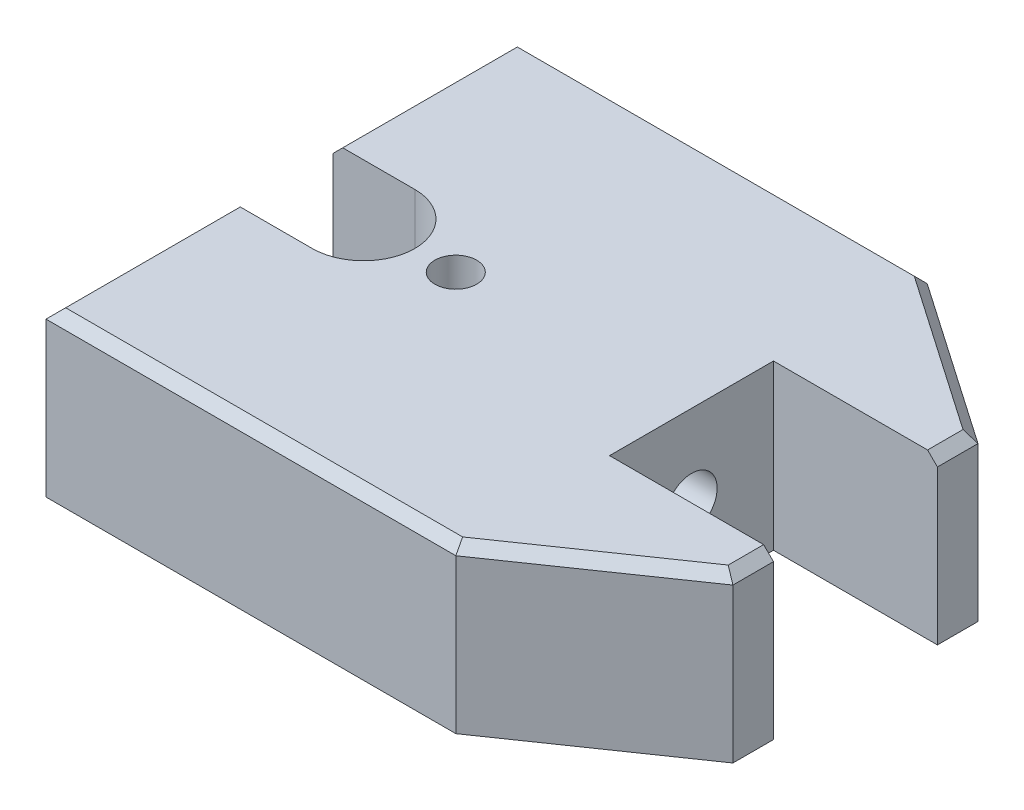
SolidWorks part; units mm, degrees
ref_plane "Front Plane" through (0, 0, 0) normal (0, 0, 1) x (1, 0, 0)
ref_plane "Top Plane" through (0, 0, 0) normal (0, 1, 0) x (1, 0, 0)
ref_plane "Right Plane" through (0, 0, 0) normal (1, 0, 0) x (0, 0, -1)
sketch "Sketch2" plane through (0, 0, 0) normal (0, 1, 0) x (1, 0, 0)
  line L0 (0, 0) -> (-73.0604, 0) construction
  line L1 (0, 36.5125) -> (0, -36.5125)
  line L2 (0, -36.5125) -> (63.5, -36.5125)
  line L3 (0, 36.5125) -> (63.5, 36.5125)
  line L4 (63.5, -36.5125) -> (88.9, -18.9865)
  line L5 (63.5, 36.5125) -> (88.9, 18.9865)
  line L6 (88.9, -18.9865) -> (88.9, 18.9865)
  point P9 (88.9, 0)
  dimension "D1" = 63.5
  dimension "D2" = 73.025
  dimension "D3" = 88.9
  dimension "D4" = 17.526
extrude "Boss-Extrude2" add sketch "Sketch2" along normal mid plane 25.4
sketch "Sketch3" plane through (0, 12.7, 0) normal (0, 1, 0) x (1, 0, 0)
  line L0 (0, 0) -> (88.9, 0) construction
  line L1 (88.9, -18.9865) -> (88.9, 18.9865) construction
  line L3 (63.5, 12.7) -> (88.9, 12.7)
  line L4 (63.5, 12.7) -> (63.5, -12.7)
  line L5 (63.5, -12.7) -> (88.9, -12.7)
  line L6 (88.9, 12.7) -> (88.9, -12.7)
  line L7 (63.5, 12.7) -> (88.9, -12.7) construction
  line L8 (63.5, -12.7) -> (88.9, 12.7) construction
  point P5 (76.2, 0)
  dimension "D1" = 25.4
  dimension "D2" = 25.4
extrude "Cut-Extrude1" cut sketch "Sketch3" against normal through all
sketch "Sketch4" plane through (0, 12.7, 0) normal (0, 1, 0) x (1, 0, 0)
  line L0 (0, 7.9375) -> (12.6873, 7.9375)
  line L1 (0, 36.5125) -> (0, -36.5125) construction
  line L2 (12.6873, -7.9375) -> (0, -7.9375)
  line L3 (0, -7.9375) -> (0, 7.9375)
  arc A0 (12.6873, 7.9375) -> (12.6873, -7.9375) centre (12.6873, 0) cw
  point P4 (20.6248, 0)
  dimension "D1" = 20.6248
  dimension "D2" = 15.875
extrude "Cut-Extrude3" cut sketch "Sketch4" against normal through all
hole_wizard "Hole1" positions "Sketch5" profile "Sketch6" legacy
sketch "Sketch5" plane through (0, 12.7, 0) normal (0, 1, 0) x (1, 0, 0)
  line L0 (0, -7.9375) -> (0, -36.5125) construction
  point P0 (26.9748, 0)
  dimension "D1" = 26.9748
sketch "Sketch6" plane through (26.9748, 12.7, 0) normal (1, 0, 0) x (0, 0, 1)
  line L0 (0, 0) -> (0, 14.2748)
  line L1 (0, 14.2748) -> (3.2385, 14.2748)
  line L2 (3.2385, 14.2748) -> (3.2385, 0)
  line L3 (3.2385, 0) -> (0, 0)
  line L4 (0, 110) -> (0, -10) construction
  dimension "Diameter" = 6.477
  dimension "Depth" = 14.2748
hole_wizard "3/8-16 Tapped Hole1" positions "Sketch7" profile "Sketch8" tap size "3/8-16" standard "ANSI Inch"
sketch "Sketch7" plane through (63.5, 0, 0) normal (1, 0, 0) x (0, 0, -1)
  point P0 (0, 0)
sketch "Sketch8" plane through (63.5, 0, 0) normal (0, 1, 0) x (0, 0, -1)
  line L0 (0, 0) -> (0, 22.7047)
  line L1 (0, 22.7047) -> (3.9687, 20.32)
  line L2 (3.9687, 20.32) -> (3.9688, 0)
  line L5 (3.9688, 0) -> (0, 0)
  line L10 (0, 22.7047) -> (-3.9688, 20.32) construction
  line L11 (0, -6.35) -> (0, 107.95) construction
  dimension "Tap Drill Dia." = 7.9375
  dimension "Tap Drill Depth" = 20.32
  dimension "Drill Angle" = 118
cosmetic thread "Hole Thread1" parameters "D1"=19.05, "D2"=9.525
chamfer "Chamfer1" distance 1.524 angle 45 8 edges at (0, 12.7, -22.225) (31.75, 12.7, -36.5125) (76.2, 12.7, -27.7495) (88.9, 12.7, -15.8433) (88.9, 12.7, 15.8432) (76.2, 12.7, 27.7495) (31.75, 12.7, 36.5125) (0, 12.7, 22.225)
